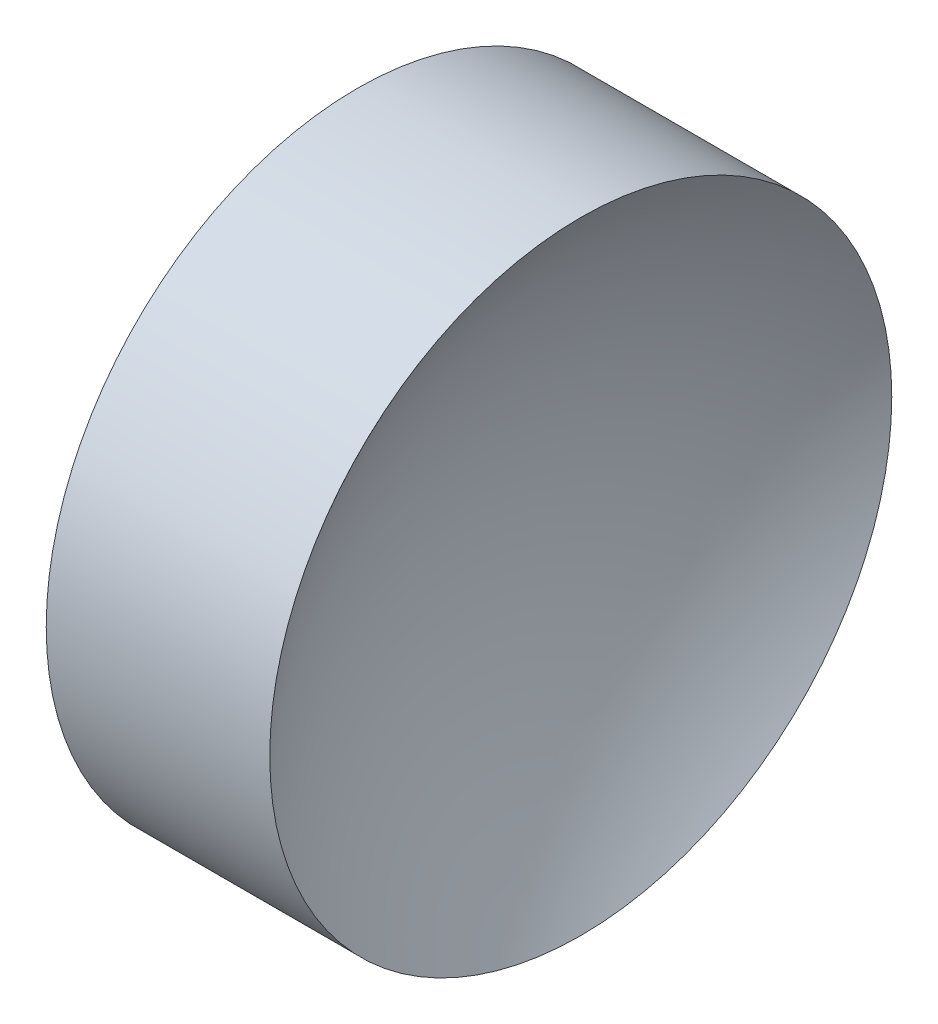
SolidWorks part; units mm, degrees
ref_plane "前视基准面" through (0, 0, 0) normal (0, 0, 1) x (1, 0, 0)
ref_plane "上视基准面" through (0, 0, 0) normal (0, 1, 0) x (1, 0, 0)
ref_plane "右视基准面" through (0, 0, 0) normal (1, 0, 0) x (0, 0, -1)
sketch "草图1" plane through (0, 0, 0) normal (0, 0, 1) x (1, 0, 0)
  line L0 (44.7821, 28.4776) -> (55.1344, 28.4776) construction
  line L1 (47.7447, 28.4776) -> (47.7447, 34.8276)
  line L2 (47.7447, 34.8276) -> (52.3087, 34.8276)
  line L3 (50.2447, 28.4776) -> (47.7447, 28.4776)
  arc A0 (52.3087, 34.8276) -> (50.2447, 28.4776) centre (61.0447, 28.4776) ccw
revolve "旋转1" add sketch "草图1" angle 360 about L0
